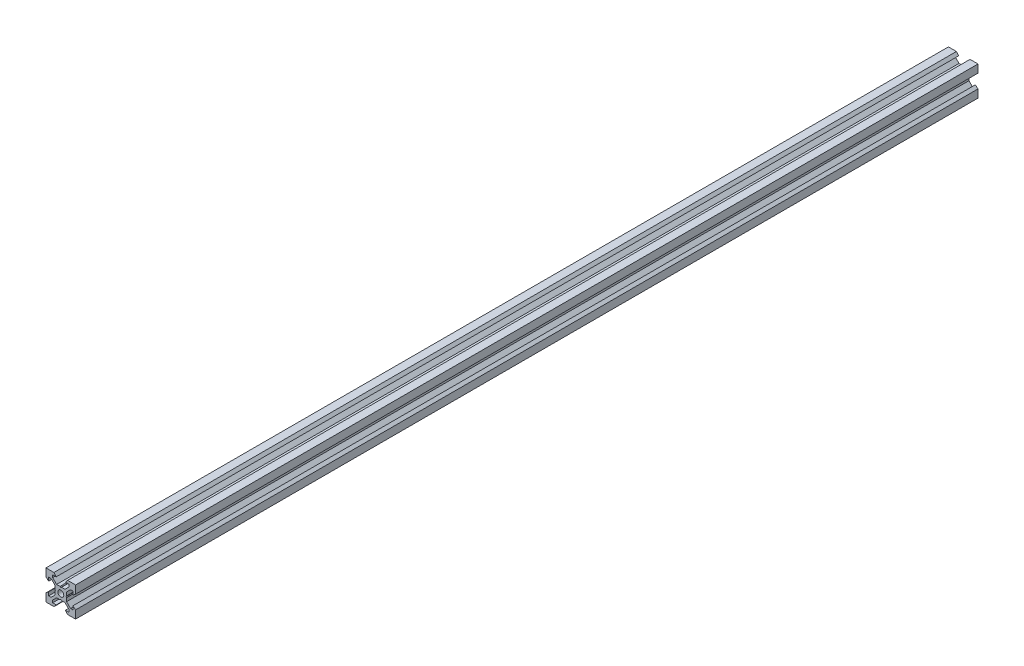
SolidWorks part; units mm, degrees
ref_plane "Front Plane" through (0, 0, 0) normal (0, 0, 1) x (1, 0, 0)
ref_plane "Top Plane" through (0, 0, 0) normal (0, 1, 0) x (1, 0, 0)
ref_plane "Right Plane" through (0, 0, 0) normal (1, 0, 0) x (0, 0, -1)
sketch "Sketch1" plane through (0, 0, 0) normal (0, 0, 1) x (1, 0, 0)
  line L0 (10, 10) -> (4.6104, 10) construction
  line L1 (10, 10) -> (10, 4.6104) construction
  line L2 (10, -10) -> (10, -4.6104) construction
  line L3 (10, -10) -> (4.6104, -10) construction
  line L4 (10, 10) -> (10, 4.6104)
  line L5 (6.5607, 5.5) -> (8.2, 5.5)
  line L6 (5.5, 8.2) -> (5.5, 6.5607)
  line L7 (10, 10) -> (4.6104, 10)
  line L8 (10, 10) -> (10, 4.6104)
  line L9 (6.5607, 5.5) -> (3.9, 2.8393)
  line L10 (5.5, 6.5607) -> (2.8393, 3.9)
  line L11 (10, 4.6104) -> (8.2, 3.1)
  line L12 (4.6104, 10) -> (3.1, 8.2)
  line L13 (8.2, 3.1) -> (8.2, 5.5)
  line L14 (3.1, 8.2) -> (5.5, 8.2)
  line L15 (-6.5607, 5.5) -> (-8.2, 5.5)
  line L16 (6.5607, -5.5) -> (8.2, -5.5)
  line L17 (3.1, -8.2) -> (5.5, -8.2)
  line L18 (8.2, -3.1) -> (8.2, -5.5)
  line L19 (4.6104, -10) -> (3.1, -8.2)
  line L20 (10, -4.6104) -> (8.2, -3.1)
  line L21 (0.5196, -3.9) -> (0, -3.6)
  line L22 (0.5196, 3.9) -> (0, 3.6)
  line L23 (3.6, 0) -> (3.9, -0.5196)
  line L24 (3.9, 0.5196) -> (3.6, 0)
  line L25 (3.9, 0.5196) -> (3.9, 2.8393)
  line L26 (2.8393, 3.9) -> (0.5196, 3.9)
  line L27 (3.9, -2.8393) -> (3.9, -0.5196)
  line L28 (2.8393, -3.9) -> (0.5196, -3.9)
  line L29 (5.5, -6.5607) -> (2.8393, -3.9)
  line L30 (6.5607, -5.5) -> (3.9, -2.8393)
  line L31 (10, -10) -> (10, -4.6104)
  line L32 (10, -10) -> (4.6104, -10)
  line L33 (5.5, -8.2) -> (5.5, -6.5607)
  line L34 (-6.5607, -5.5) -> (-8.2, -5.5)
  line L35 (10, -10) -> (10, -4.6104)
  line L36 (0, 0) -> (0, 8.2) construction
  line L37 (-10, -10) -> (-4.6104, -10) construction
  line L38 (-10, -10) -> (-10, -4.6104) construction
  line L39 (-10, 10) -> (-10, 4.6104) construction
  line L40 (-10, 10) -> (-4.6104, 10) construction
  line L41 (-10, -10) -> (-10, -4.6104)
  line L43 (-5.5, -8.2) -> (-5.5, -6.5607)
  line L44 (-10, -10) -> (-4.6104, -10)
  line L45 (-10, -10) -> (-10, -4.6104)
  line L46 (-6.5607, -5.5) -> (-3.9, -2.8393)
  line L47 (-5.5, -6.5607) -> (-2.8393, -3.9)
  line L48 (-2.8393, -3.9) -> (-0.5196, -3.9)
  line L49 (-3.9, -2.8393) -> (-3.9, -0.5196)
  line L50 (-2.8393, 3.9) -> (-0.5196, 3.9)
  line L51 (-3.9, 0.5196) -> (-3.9, 2.8393)
  line L52 (-3.9, 0.5196) -> (-3.6, 0)
  line L53 (-3.6, 0) -> (-3.9, -0.5196)
  line L54 (-0.5196, 3.9) -> (0, 3.6)
  line L55 (-0.5196, -3.9) -> (0, -3.6)
  line L56 (-10, -4.6104) -> (-8.2, -3.1)
  line L57 (-4.6104, -10) -> (-3.1, -8.2)
  line L58 (-8.2, -3.1) -> (-8.2, -5.5)
  line L59 (-3.1, -8.2) -> (-5.5, -8.2)
  line L60 (-10, -10) -> (10, -10) construction
  line L61 (-10, -10) -> (-10, 10) construction
  line L62 (-3.1, 8.2) -> (-5.5, 8.2)
  line L63 (-8.2, 3.1) -> (-8.2, 5.5)
  line L64 (-4.6104, 10) -> (-3.1, 8.2)
  line L65 (-10, 4.6104) -> (-8.2, 3.1)
  line L66 (-5.5, 6.5607) -> (-2.8393, 3.9)
  line L67 (-6.5607, 5.5) -> (-3.9, 2.8393)
  line L68 (-10, 10) -> (-10, 4.6104)
  line L69 (-10, 10) -> (-4.6104, 10)
  line L70 (-5.5, 8.2) -> (-5.5, 6.5607)
  line L71 (-10, 10) -> (10, 10) construction
  line L72 (-10, 10) -> (-10, 4.6104)
  line L73 (10, -10) -> (10, 10) construction
  line L74 (-10, -10) -> (10, 10) construction
  line L75 (-10, 10) -> (10, -10) construction
  circle A0 centre (0, 0) radius 2
  dimension "D7" = 4
  dimension "D1" = 20
  dimension "D2" = 5.3896
  dimension "D3" = 4.5
  dimension "D4" = 50
  dimension "D5" = 1.8
  dimension "D6" = 1.5104
  dimension "D8" = 5.5
  dimension "D9" = 120
  dimension "D10" = 0.3
  dimension "D11" = 2.3197
  dimension "D12" = 7.8
  dimension "D13" = 7.8
  dimension "D14" = 1.5
  dimension "D15" = 2.6607
extrude "Boss-Extrude1" add sketch "Sketch1" along normal mid plane 610 contours L70 L62 L64 L69 L68 L65 L63 L15 L67 L51 L52 L53 L49 L46 L34 L58 L56 L41 L44 L57 L59 L43 L47 L48 L55 L21 L28 L29 L33 L17 L19 L32 L31 L20 L18 L16 L30 L27 L23 L24 L25 L9 L5 L13 L11 L4 L7 L12 L14 L6 L10
